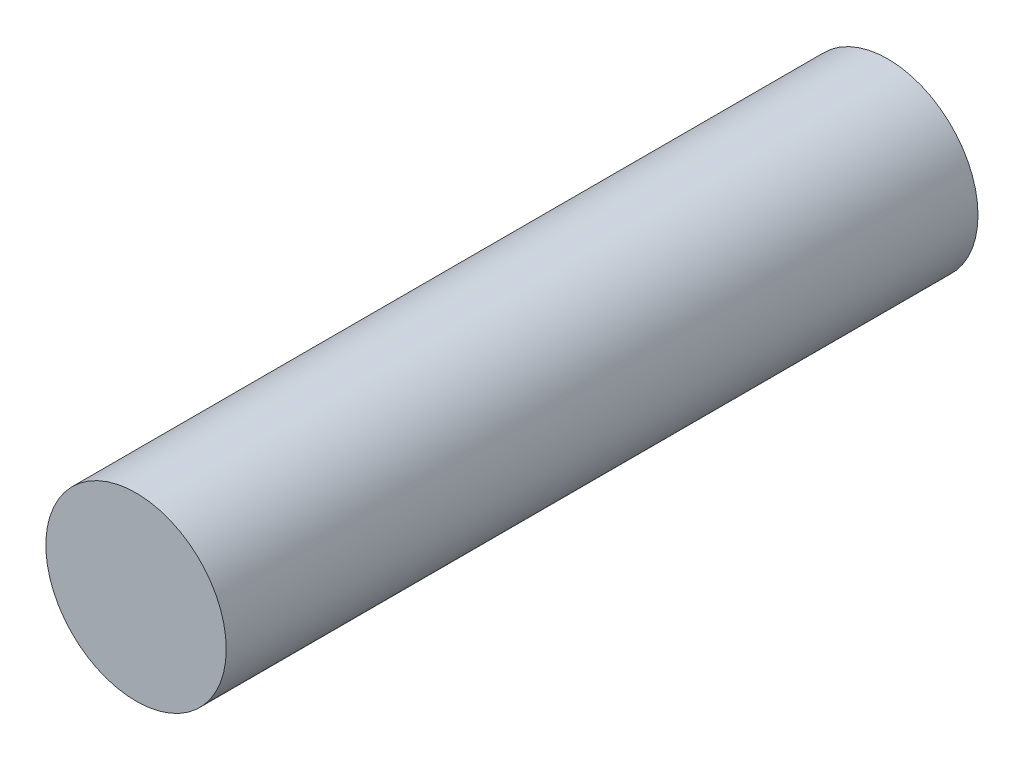
SolidWorks part; units mm, degrees
ref_plane "Front Plane" through (0, 0, 0) normal (0, 0, 1) x (1, 0, 0)
ref_plane "Top Plane" through (0, 0, 0) normal (0, 1, 0) x (1, 0, 0)
ref_plane "Right Plane" through (0, 0, 0) normal (1, 0, 0) x (0, 0, -1)
sketch "Sketch1" plane through (0, 0, 0) normal (0, 0, 1) x (1, 0, 0)
  circle A0 centre (0, 0) radius 6
  dimension "D1" = 12
extrude "Boss-Extrude1" add sketch "Sketch1" along normal blind 50
